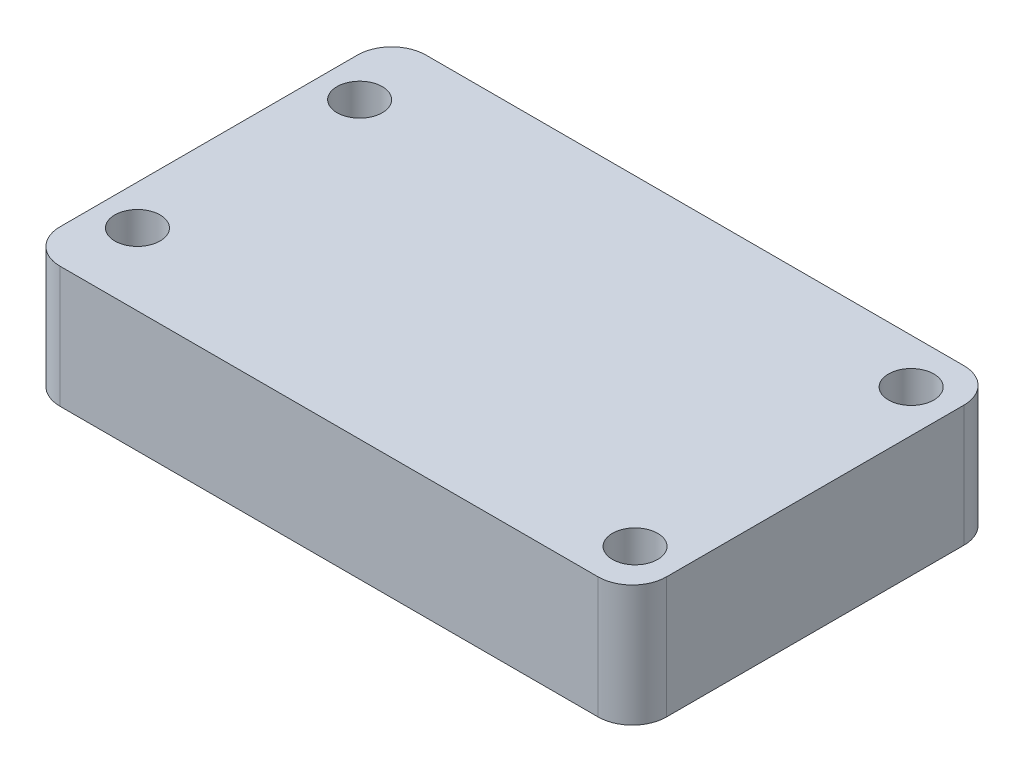
SolidWorks part; units mm, degrees
ref_plane "Front Plane" through (0, 0, 0) normal (0, 0, 1) x (1, 0, 0)
ref_plane "Top Plane" through (0, 0, 0) normal (0, 1, 0) x (1, 0, 0)
ref_plane "Right Plane" through (0, 0, 0) normal (1, 0, 0) x (0, 0, -1)
sketch "Sketch1" plane through (0, 0, 0) normal (0, 1, 0) x (1, 0, 0)
  line L1 (-91.4484, -9.3567) -> (-55.4058, -9.3567)
  line L2 (-91.4484, -9.3567) -> (-91.4484, 12.3857)
  line L3 (-91.4484, 12.3857) -> (-55.4058, 12.3857)
  line L4 (-55.4058, -9.3567) -> (-55.4058, 12.3857)
  dimension "D1" = 36.0426
  dimension "D2" = 21.7424
extrude "Boss-Extrude1" add sketch "Sketch1" along normal blind 7.2136
sketch "Sketch2" plane through (0, 7.2136, 0) normal (0, 1, 0) x (1, 0, 0)
  line L0 (-55.4058, -9.3567) -> (-55.4058, 12.3857) construction
  line L1 (-55.4058, 12.3857) -> (-91.4484, 12.3857) construction
  line L2 (-91.4484, 12.3857) -> (-91.4484, -9.3567) construction
  line L3 (-91.4484, 1.5145) -> (-55.4058, 1.5145) construction
  circle A0 centre (-57.9077, 9.7187) radius 1.3462
  circle A1 centre (-89.0862, 8.1185) radius 1.3462
  circle A2 centre (-57.9077, -6.6897) radius 1.3462
  circle A3 centre (-89.0862, -5.0895) radius 1.3462
  dimension "D1" = 2.5019
  dimension "D2" = 2.667
  dimension "D3" = 2.3622
  dimension "D4" = 4.2672
extrude "Cut-Extrude1" cut sketch "Sketch2" against normal blind 7.2136
fillet "Fillet1" radius 2.032 4 edges at (-55.4058, 3.6068, 9.3567) (-55.4058, 3.6068, -12.3857) (-91.4484, 3.6068, 9.3567) (-91.4484, 3.6068, -12.3857)
sketch "Sketch3" plane through (0, 0, 0) normal (0, -1, 0) x (1, 0, 0)
  line L0 (-73.4271, 9.3567) -> (-73.4271, -23.8466) construction
  line L1 (-89.4164, 9.3567) -> (-57.4378, 9.3567) construction
